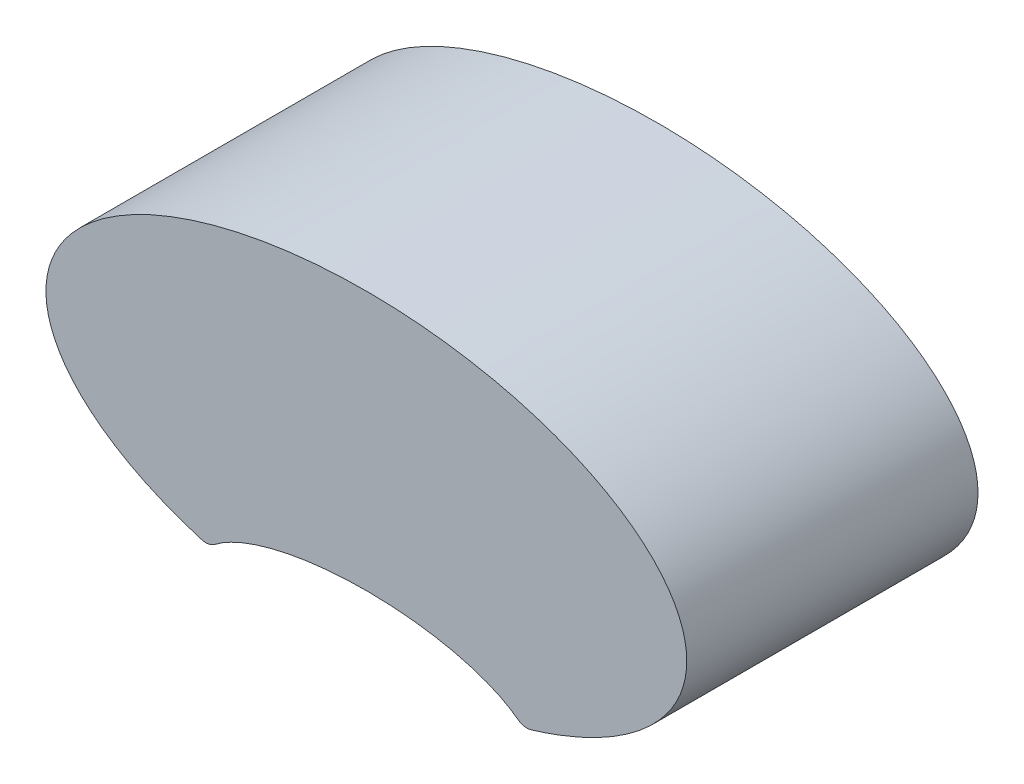
SolidWorks part; units mm, degrees
ref_plane "Alzado" through (0, 0, 0) normal (0, 0, 1) x (1, 0, 0)
ref_plane "Planta" through (0, 0, 0) normal (0, 1, 0) x (1, 0, 0)
ref_plane "Vista lateral" through (0, 0, 0) normal (1, 0, 0) x (0, 0, -1)
sketch "Croquis2" plane through (0, 0, 0) normal (0, 0, 1) x (1, 0, 0)
  line L0 (1.5756, 0.3058) -> (1.4514, 0.3058)
  line L1 (0, -0.9979) -> (0, 1.8615) construction
  line L2 (-1.5756, 0.1352) -> (-1.3036, 0.1352)
  line L3 (-0.9046, 0.1352) -> (-0.5353, 0.1352)
  line L4 (-1.5756, 0.3058) -> (-1.4514, 0.3058)
  line L5 (0.9046, 0.1352) -> (0.5353, 0.1352)
  line L6 (1.5756, 0.1352) -> (1.3036, 0.1352)
  arc A0 (-1.5756, 0.3058) -> (-1.5756, 0.1352) centre (-1.5756, 0.2205) ccw
  arc A1 (-1.5, 0.6873) -> (-1.4786, 0.8608) centre (-1.3653, 0.7588) cw
  arc A2 (-1.4786, 0.8608) -> (-1.3442, 0.9386) centre (-1.2911, 0.6919) cw
  arc A3 (-1.4514, 0.3058) -> (-1.4027, 0.3266) centre (-1.4514, 0.3733) ccw
  arc A4 (1.3171, 0.9546) -> (-1.3171, 0.9546) centre (0, -0.1967) ccw
  arc A9 (-0.5653, 0.3099) -> (-0.5205, 0.3181) centre (-0.551, 0.3578) ccw
  arc A10 (-0.5226, 0.1245) -> (-0.5535, 0.1352) centre (-0.5535, 0.0852) ccw
  arc A11 (-0.8922, 0.1352) -> (-0.9146, 0.1299) centre (-0.8922, 0.0852) ccw
  arc A12 (-1.2935, 0.1299) -> (-1.316, 0.1352) centre (-1.316, 0.0852) ccw
  arc A13 (-1.3442, 0.9386) -> (-1.3171, 0.9546) centre (-1.3548, 0.9875) ccw
  arc A14 (1.3442, 0.9386) -> (1.3171, 0.9546) centre (1.3548, 0.9875) cw
  arc A15 (1.2935, 0.1299) -> (1.316, 0.1352) centre (1.316, 0.0852) cw
  arc A16 (0.8922, 0.1352) -> (0.9146, 0.1299) centre (0.8922, 0.0852) cw
  arc A17 (0.5226, 0.1245) -> (0.5535, 0.1352) centre (0.5535, 0.0852) cw
  arc A18 (0.5653, 0.3099) -> (0.5205, 0.3181) centre (0.551, 0.3578) cw
  arc A19 (1.4514, 0.3058) -> (1.4027, 0.3266) centre (1.4514, 0.3733) cw
  arc A20 (1.4786, 0.8608) -> (1.3442, 0.9386) centre (1.2911, 0.6919) ccw
  arc A21 (1.5, 0.6873) -> (1.4786, 0.8608) centre (1.3653, 0.7588) ccw
  arc A22 (1.5756, 0.3058) -> (1.5756, 0.1352) centre (1.5756, 0.2205) cw
  ellipse E0 centre (1.1041, 0.2205) end of major axis (0.8393, 0.2205) minor radius 0.1297 (1.3036, 0.1352) -> (0.9046, 0.1352) cw
  ellipse E1 centre (0, 0.7817) end of major axis (1.1, 0.7817) minor radius 0.55 (0.5653, 0.3099) -> (-0.5653, 0.3099) ccw
  ellipse E2 centre (0, 0.2205) end of major axis (0.5805, 0.2205) minor radius 0.2205 (-0.5353, 0.1352) -> (0.5353, 0.1352) ccw
  ellipse E3 centre (-1.1041, 0.2205) end of major axis (-0.8393, 0.2205) minor radius 0.1297 (-1.3036, 0.1352) -> (-0.9046, 0.1352) ccw
  ellipse E4 centre (0, 0.2205) end of major axis (0.5805, 0.2205) minor radius 0.2205 (0.5205, 0.3181) -> (-0.5205, 0.3181) ccw
  ellipse E5 centre (0, 0.2205) end of major axis (0.5805, 0.2205) minor radius 0.2205 (-0.5353, 0.1352) -> (0, 0) ccw
  spline S0 degree 3 poles (-1.4027, 0.3266) (-1.3601, 0.3709) (-1.2731, 0.4746) (-1.4058, 0.5099) (-1.5, 0.6873) knots 0.042799 0.042799 0.042799 0.042799 0.330664 1 1 1 1
  spline S1 degree 3 poles (1.4027, 0.3266) (1.3601, 0.3709) (1.2731, 0.4746) (1.4058, 0.5099) (1.5, 0.6873) knots 0.042799 0.042799 0.042799 0.042799 0.330664 1 1 1 1
  point P3 (0, 0)
  point P6 (0, 1.3317)
  point P42 (0, 0.441)
  dimension "D2" = 1.1
  dimension "D4" = 0.1
  dimension "D5" = 0.1
  dimension "D6" = 0.1
  dimension "D7" = 0.1
  dimension "D8" = 0.1
  dimension "D1" = 1.5
  dimension "D3" = 2.2
extrude "Saliente-Extruir2" add sketch "Croquis2" against normal blind 1 contours E2 L1 E4 A9 E1 A4 A13 A2 A1 S0 A3 L4 A0 L2 E3 L3 | L1 E2 L5 E0 L6 A22 L0 A19 S1 A21 A20 A14 A4 E1 A18 E4
sketch "Croquis5" plane through (0, 0, 0) normal (0, 0, 1) x (1, 0, 0)
  line L6 (0.5353, 0.1352) -> (0.9046, 0.1352)
  line L7 (1.3036, 0.1352) -> (1.5756, 0.1352)
  line L8 (1.5756, 0.3058) -> (1.4514, 0.3058)
  line L9 (-1.4514, 0.3058) -> (-1.5756, 0.3058)
  line L10 (-1.5756, 0.1352) -> (-1.3036, 0.1352)
  line L11 (-0.9046, 0.1352) -> (-0.5353, 0.1352)
  line L12 (0.5353, 0.1352) -> (0.9046, 0.1352)
  line L13 (1.3036, 0.1352) -> (1.5756, 0.1352)
  line L14 (1.5756, 0.3058) -> (1.4514, 0.3058)
  line L15 (-1.4514, 0.3058) -> (-1.5756, 0.3058)
  line L16 (-1.5756, 0.1352) -> (-1.3036, 0.1352)
  line L17 (-0.9046, 0.1352) -> (-0.5353, 0.1352)
  arc A0 (0.5205, 0.3181) -> (0.5653, 0.3099) centre (0.551, 0.3578) ccw construction
  arc A1 (-0.5653, 0.3099) -> (-0.5205, 0.3181) centre (-0.551, 0.3578) ccw construction
  arc A2 (0.5205, 0.3181) -> (0.5653, 0.3099) centre (0.551, 0.3578) ccw
  arc A3 (-0.5653, 0.3099) -> (-0.5205, 0.3181) centre (-0.551, 0.3578) ccw
  arc A11 (1.5756, 0.1352) -> (1.5756, 0.3058) centre (1.5756, 0.2205) ccw
  arc A12 (1.4027, 0.3266) -> (1.4514, 0.3058) centre (1.4514, 0.3733) ccw
  arc A13 (1.5, 0.6873) -> (1.4786, 0.8608) centre (1.3653, 0.7588) ccw
  arc A14 (1.4786, 0.8608) -> (1.3442, 0.9386) centre (1.2911, 0.6919) ccw
  arc A15 (1.3171, 0.9546) -> (1.3442, 0.9386) centre (1.3548, 0.9875) ccw
  arc A16 (1.3171, 0.9546) -> (-1.3171, 0.9546) centre (0, -0.1967) ccw
  arc A17 (-1.3442, 0.9386) -> (-1.3171, 0.9546) centre (-1.3548, 0.9875) ccw
  arc A18 (-1.3442, 0.9386) -> (-1.4786, 0.8608) centre (-1.2911, 0.6919) ccw
  arc A19 (-1.4786, 0.8608) -> (-1.5, 0.6873) centre (-1.3653, 0.7588) ccw
  arc A20 (-1.4514, 0.3058) -> (-1.4027, 0.3266) centre (-1.4514, 0.3733) ccw
  arc A21 (-1.5756, 0.3058) -> (-1.5756, 0.1352) centre (-1.5756, 0.2205) ccw
  arc A22 (1.5756, 0.1352) -> (1.5756, 0.3058) centre (1.5756, 0.2205) ccw
  arc A23 (1.4027, 0.3266) -> (1.4514, 0.3058) centre (1.4514, 0.3733) ccw
  arc A24 (1.5, 0.6873) -> (1.4786, 0.8608) centre (1.3653, 0.7588) ccw
  arc A25 (1.4786, 0.8608) -> (1.3442, 0.9386) centre (1.2911, 0.6919) ccw
  arc A26 (1.3171, 0.9546) -> (1.3442, 0.9386) centre (1.3548, 0.9875) ccw
  arc A27 (1.3171, 0.9546) -> (-1.3171, 0.9546) centre (0, -0.1967) ccw
  arc A28 (-1.3442, 0.9386) -> (-1.3171, 0.9546) centre (-1.3548, 0.9875) ccw
  arc A29 (-1.3442, 0.9386) -> (-1.4786, 0.8608) centre (-1.2911, 0.6919) ccw
  arc A30 (-1.4786, 0.8608) -> (-1.5, 0.6873) centre (-1.3653, 0.7588) ccw
  arc A31 (-1.4514, 0.3058) -> (-1.4027, 0.3266) centre (-1.4514, 0.3733) ccw
  arc A32 (-1.5756, 0.3058) -> (-1.5756, 0.1352) centre (-1.5756, 0.2205) ccw
  ellipse E0 centre (0, 0.2205) end of major axis (0.5805, 0.2205) minor radius 0.2205 (0.5205, 0.3181) -> (-0.5205, 0.3181) ccw construction
  ellipse E1 centre (0, 0.7817) end of major axis (1.1, 0.7817) minor radius 0.55 (0.5653, 0.3099) -> (-0.5653, 0.3099) ccw construction
  ellipse E2 centre (0, 0.2205) end of major axis (0.5805, 0.2205) minor radius 0.2205 (0.5205, 0.3181) -> (-0.5205, 0.3181) ccw
  ellipse E3 centre (0, 0.2205) end of major axis (0.5805, 0.2205) minor radius 0.2205 (-0.5353, 0.1352) -> (0.5353, 0.1352) ccw
  ellipse E4 centre (1.1041, 0.2205) end of major axis (0.8393, 0.2205) minor radius 0.1297 (0.9046, 0.1352) -> (1.3036, 0.1352) ccw
  ellipse E5 centre (-1.1041, 0.2205) end of major axis (-0.8393, 0.2205) minor radius 0.1297 (-1.3036, 0.1352) -> (-0.9046, 0.1352) ccw
  ellipse E6 centre (0, 0.2205) end of major axis (0.5805, 0.2205) minor radius 0.2205 (-0.5353, 0.1352) -> (0.5353, 0.1352) ccw
  ellipse E7 centre (1.1041, 0.2205) end of major axis (0.8393, 0.2205) minor radius 0.1297 (0.9046, 0.1352) -> (1.3036, 0.1352) ccw
  ellipse E8 centre (-1.1041, 0.2205) end of major axis (-0.8393, 0.2205) minor radius 0.1297 (-1.3036, 0.1352) -> (-0.9046, 0.1352) ccw
  ellipse E9 centre (0, 0.7817) end of major axis (1.1, 0.7817) minor radius 0.55 (0.5653, 0.3099) -> (-0.5653, 0.3099) ccw
  spline S2 degree 3 poles (-1432.0818, -3731.1505) (130.0539, -43.2962) (-98.2119, 30.9761) (78.2919, -20.6265) (-1831.4926, 3555.1761) knots -22.744342 -22.744342 -22.744342 -22.744342 0.330664 18.33491 18.33491 18.33491 18.33491 only from (1.4027, 0.3266) to (1.5, 0.6873)
  spline S3 degree 3 poles (1831.5289, 3555.2439) (-78.2929, -20.6267) (98.2121, 30.9762) (-130.0528, -43.2958) (1432.061, -3731.1013) knots -17.292225 -17.292225 -17.292225 -17.292225 0.712135 23.787039 23.787039 23.787039 23.787039 only from (-1.5, 0.6873) to (-1.4027, 0.3266)
  spline S4 degree 3 poles (1.4027, 0.3266) (1.3601, 0.3709) (1.2731, 0.4746) (1.4058, 0.5099) (1.5, 0.6873) knots 0.042799 0.042799 0.042799 0.042799 0.330664 1 1 1 1
  spline S5 degree 3 poles (-1.5, 0.6873) (-1.4058, 0.5099) (-1.2731, 0.4746) (-1.3601, 0.3709) (-1.4027, 0.3266) knots 0.042799 0.042799 0.042799 0.042799 0.712135 1 1 1 1
  dimension "D1" = 0
extrude "Saliente-Extruir4" add sketch "Croquis5" against normal up to surface (1 mm away) separate body contours A2 E9 A3 E2 up to face at (0, 0.5975, -1)
sketch "Croquis6" plane through (0, 0, 0) normal (0, 0, 1) x (1, 0, 0)
  line L0 (0.5353, 0.1352) -> (0.9046, 0.1352) construction
  line L1 (1.3036, 0.1352) -> (1.5756, 0.1352) construction
  line L2 (1.5756, 0.3058) -> (1.4514, 0.3058) construction
  line L3 (-1.4514, 0.3058) -> (-1.5756, 0.3058) construction
  line L4 (-1.5756, 0.1352) -> (-1.3036, 0.1352) construction
  line L5 (-0.9046, 0.1352) -> (-0.5353, 0.1352) construction
  line L6 (0.5353, 0.1352) -> (0.9046, 0.1352)
  line L7 (1.3036, 0.1352) -> (1.5756, 0.1352)
  line L8 (1.5756, 0.3058) -> (1.4514, 0.3058)
  line L9 (-1.4514, 0.3058) -> (-1.5756, 0.3058)
  line L10 (-1.5756, 0.1352) -> (-1.3036, 0.1352)
  line L11 (-0.9046, 0.1352) -> (-0.5353, 0.1352)
  arc A0 (1.5756, 0.1352) -> (1.5756, 0.3058) centre (1.5756, 0.2205) ccw construction
  arc A1 (1.4027, 0.3266) -> (1.4514, 0.3058) centre (1.4514, 0.3733) ccw construction
  arc A2 (1.5, 0.6873) -> (1.4786, 0.8608) centre (1.3653, 0.7588) ccw construction
  arc A3 (1.4786, 0.8608) -> (1.3442, 0.9386) centre (1.2911, 0.6919) ccw construction
  arc A4 (1.3171, 0.9546) -> (1.3442, 0.9386) centre (1.3548, 0.9875) ccw construction
  arc A5 (1.3171, 0.9546) -> (-1.3171, 0.9546) centre (0, -0.1967) ccw construction
  arc A6 (-1.3442, 0.9386) -> (-1.3171, 0.9546) centre (-1.3548, 0.9875) ccw construction
  arc A7 (-1.3442, 0.9386) -> (-1.4786, 0.8608) centre (-1.2911, 0.6919) ccw construction
  arc A8 (-1.4786, 0.8608) -> (-1.5, 0.6873) centre (-1.3653, 0.7588) ccw construction
  arc A9 (-1.4514, 0.3058) -> (-1.4027, 0.3266) centre (-1.4514, 0.3733) ccw construction
  arc A10 (-1.5756, 0.3058) -> (-1.5756, 0.1352) centre (-1.5756, 0.2205) ccw construction
  arc A11 (0.5205, 0.3181) -> (0.5653, 0.3099) centre (0.551, 0.3578) ccw construction
  arc A12 (-0.5653, 0.3099) -> (-0.5205, 0.3181) centre (-0.551, 0.3578) ccw construction
  arc A13 (1.5756, 0.1352) -> (1.5756, 0.3058) centre (1.5756, 0.2205) ccw
  arc A14 (1.4027, 0.3266) -> (1.4514, 0.3058) centre (1.4514, 0.3733) ccw
  arc A15 (1.5, 0.6873) -> (1.4786, 0.8608) centre (1.3653, 0.7588) ccw
  arc A16 (1.4786, 0.8608) -> (1.3442, 0.9386) centre (1.2911, 0.6919) ccw
  arc A17 (1.3171, 0.9546) -> (1.3442, 0.9386) centre (1.3548, 0.9875) ccw
  arc A18 (1.3171, 0.9546) -> (-1.3171, 0.9546) centre (0, -0.1967) ccw
  arc A19 (-1.3442, 0.9386) -> (-1.3171, 0.9546) centre (-1.3548, 0.9875) ccw
  arc A20 (-1.3442, 0.9386) -> (-1.4786, 0.8608) centre (-1.2911, 0.6919) ccw
  arc A21 (-1.4786, 0.8608) -> (-1.5, 0.6873) centre (-1.3653, 0.7588) ccw
  arc A22 (-1.4514, 0.3058) -> (-1.4027, 0.3266) centre (-1.4514, 0.3733) ccw
  arc A23 (-1.5756, 0.3058) -> (-1.5756, 0.1352) centre (-1.5756, 0.2205) ccw
  arc A24 (0.5205, 0.3181) -> (0.5653, 0.3099) centre (0.551, 0.3578) ccw
  arc A25 (-0.5653, 0.3099) -> (-0.5205, 0.3181) centre (-0.551, 0.3578) ccw
  ellipse E0 centre (0, 0.2205) end of major axis (0.5805, 0.2205) minor radius 0.2205 (-0.5353, 0.1352) -> (0.5353, 0.1352) ccw construction
  ellipse E1 centre (1.1041, 0.2205) end of major axis (0.8393, 0.2205) minor radius 0.1297 (0.9046, 0.1352) -> (1.3036, 0.1352) ccw construction
  ellipse E2 centre (-1.1041, 0.2205) end of major axis (-0.8393, 0.2205) minor radius 0.1297 (-1.3036, 0.1352) -> (-0.9046, 0.1352) ccw construction
  ellipse E3 centre (0, 0.7817) end of major axis (1.1, 0.7817) minor radius 0.55 (0.5653, 0.3099) -> (-0.5653, 0.3099) ccw construction
  ellipse E4 centre (0, 0.2205) end of major axis (0.5805, 0.2205) minor radius 0.2205 (0.5205, 0.3181) -> (-0.5205, 0.3181) ccw construction
  ellipse E5 centre (0, 0.2205) end of major axis (0.5805, 0.2205) minor radius 0.2205 (-0.5353, 0.1352) -> (0.5353, 0.1352) ccw
  ellipse E6 centre (1.1041, 0.2205) end of major axis (0.8393, 0.2205) minor radius 0.1297 (0.9046, 0.1352) -> (1.3036, 0.1352) ccw
  ellipse E7 centre (-1.1041, 0.2205) end of major axis (-0.8393, 0.2205) minor radius 0.1297 (-1.3036, 0.1352) -> (-0.9046, 0.1352) ccw
  ellipse E8 centre (0, 0.7817) end of major axis (1.1, 0.7817) minor radius 0.55 (0.5653, 0.3099) -> (-0.5653, 0.3099) ccw
  ellipse E9 centre (0, 0.2205) end of major axis (0.5805, 0.2205) minor radius 0.2205 (0.5205, 0.3181) -> (-0.5205, 0.3181) ccw
  spline S0 degree 3 poles (-1044.9552, -2809.1333) (107.6964, -36.0062) (-80.9516, 25.6472) (64.9667, -16.7425) (-1361.6117, 2672.5847) knots -20.636716 -20.636716 -20.636716 -20.636716 0.330664 16.71062 16.71062 16.71062 16.71062 only from (1.4027, 0.3266) to (1.5, 0.6873) construction
  spline S1 degree 3 poles (1361.6193, 2672.5989) (-64.9669, -16.7425) (80.9519, 25.6473) (-107.6969, -36.0064) (1044.962, -2809.1495) knots -15.66785 -15.66785 -15.66785 -15.66785 0.712135 21.679557 21.679557 21.679557 21.679557 only from (-1.5, 0.6873) to (-1.4027, 0.3266) construction
  spline S2 degree 3 poles (1.4027, 0.3266) (1.3601, 0.3709) (1.2731, 0.4746) (1.4058, 0.5099) (1.5, 0.6873) knots 0.042799 0.042799 0.042799 0.042799 0.330664 1 1 1 1
  spline S3 degree 3 poles (-1.5, 0.6873) (-1.4058, 0.5099) (-1.2731, 0.4746) (-1.3601, 0.3709) (-1.4027, 0.3266) knots 0.042799 0.042799 0.042799 0.042799 0.712135 1 1 1 1
extrude "Cortar-Extruir5" cut sketch "Croquis6" against normal blind 10
